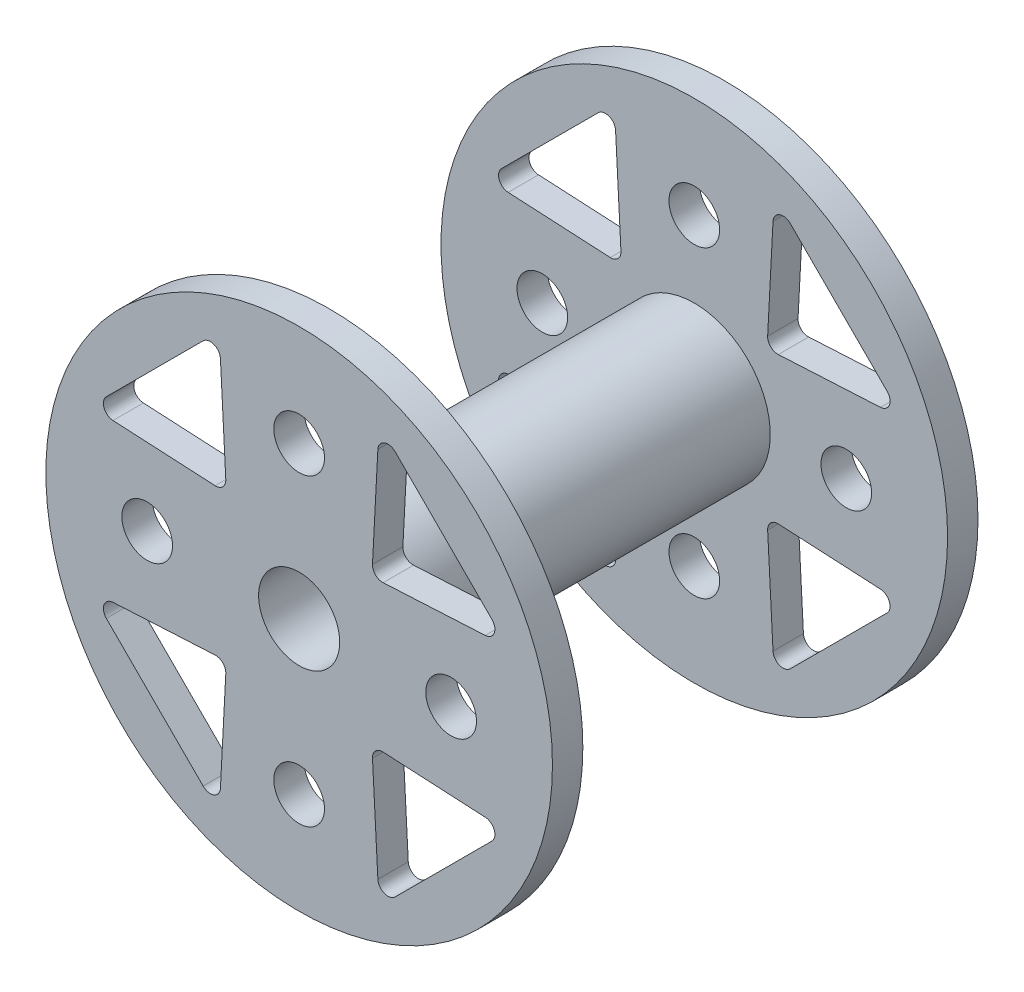
SolidWorks part; units mm, degrees
ref_plane "Alzado" through (0, 0, 0) normal (0, 0, 1) x (1, 0, 0)
ref_plane "Planta" through (0, 0, 0) normal (0, 1, 0) x (1, 0, 0)
ref_plane "Vista lateral" through (0, 0, 0) normal (1, 0, 0) x (0, 0, -1)
sketch "Croquis1" plane through (0, 0, 0) normal (0, 0, 1) x (1, 0, 0)
  circle A0 centre (0, 0) radius 4
  circle A1 centre (0, 0) radius 7.5
  dimension "D1" = 8
  dimension "D2" = 15
extrude "Saliente-Extruir1" add sketch "Croquis1" along normal blind 36
sketch "Croquis2" plane through (0, 0, 36) normal (0, 0, 1) x (1, 0, 0)
  line L0 (0, 0) -> (-17.6777, 17.6777) construction
  line L1 (-15, 0) -> (0, 0) construction
  line L2 (-19.0278, 9.4753) -> (-9.4753, 19.0278)
  line L3 (-18.3733, 7.7696) -> (-8.2901, 7.2389)
  line L4 (-7.2389, 8.2901) -> (-7.7696, 18.3733)
  line L5 (7.7696, 18.3733) -> (7.2389, 8.2901)
  line L6 (9.4753, 19.0278) -> (19.0278, 9.4753)
  line L7 (8.2901, 7.2389) -> (18.3733, 7.7696)
  line L8 (18.3733, -7.7696) -> (8.2901, -7.2389)
  line L9 (19.0278, -9.4753) -> (9.4753, -19.0278)
  line L10 (7.2389, -8.2901) -> (7.7696, -18.3733)
  line L11 (-7.7696, -18.3733) -> (-7.2389, -8.2901)
  line L12 (-9.4753, -19.0278) -> (-19.0278, -9.4753)
  line L13 (-8.2901, -7.2389) -> (-18.3733, -7.7696)
  circle A0 centre (0, 0) radius 25
  circle A1 centre (0, 0) radius 4
  arc A2 (-8.2901, 7.2389) -> (-7.2389, 8.2901) centre (-8.2375, 8.2375) ccw
  circle A3 centre (0, 0) radius 15 construction
  circle A4 centre (0, 0) radius 4 construction
  circle A5 centre (0, 15) radius 2.5
  circle A6 centre (15, 0) radius 2.5
  circle A7 centre (0, -15) radius 2.5
  circle A8 centre (-15, 0) radius 2.5
  arc A9 (-9.4753, 19.0278) -> (-7.7696, 18.3733) centre (-8.7682, 18.3207) cw
  arc A10 (-19.0278, 9.4753) -> (-18.3733, 7.7696) centre (-18.3207, 8.7682) ccw
  arc A11 (9.4753, 19.0278) -> (7.7696, 18.3733) centre (8.7682, 18.3207) ccw
  arc A12 (19.0278, 9.4753) -> (18.3733, 7.7696) centre (18.3207, 8.7682) cw
  arc A13 (7.2389, 8.2901) -> (8.2901, 7.2389) centre (8.2375, 8.2375) ccw
  arc A14 (19.0278, -9.4753) -> (18.3733, -7.7696) centre (18.3207, -8.7682) ccw
  arc A15 (9.4753, -19.0278) -> (7.7696, -18.3733) centre (8.7682, -18.3207) cw
  arc A16 (8.2901, -7.2389) -> (7.2389, -8.2901) centre (8.2375, -8.2375) ccw
  arc A17 (-9.4753, -19.0278) -> (-7.7696, -18.3733) centre (-8.7682, -18.3207) ccw
  arc A18 (-19.0278, -9.4753) -> (-18.3733, -7.7696) centre (-18.3207, -8.7682) cw
  arc A19 (-7.2389, -8.2901) -> (-8.2901, -7.2389) centre (-8.2375, -8.2375) ccw
  point P18 (0, 0)
  point P23 (-7.1805, 7.1805)
  point P26 (-7.8876, 20.6156)
  point P29 (-20.6156, 7.8876)
  point P59 (0, 0)
  dimension "D1" = 50
  dimension "D2" = 30
  dimension "D3" = 5
  dimension "D9" = 1
  dimension "D5" = 45
  dimension "D6" = 9
  dimension "D7" = 9
  dimension "D8" = 10
  dimension "D4" = 4
  dimension "D10" = 4
extrude "Saliente-Extruir2" add sketch "Croquis2" along normal blind 3
ref_plane "Plano1" through (0, 0, 18) normal (0, 0, -1) x (-1, 0, 0)
mirror "Simetría1" about plane through (0, 0, 18) normal (0, 0, -1) of "Saliente-Extruir2"
sketch "Croquis3" plane through (0, 0, 39) normal (0, 0, 1) x (1, 0, 0)
  circle A0 centre (0, -1.5461) radius 58.7682
